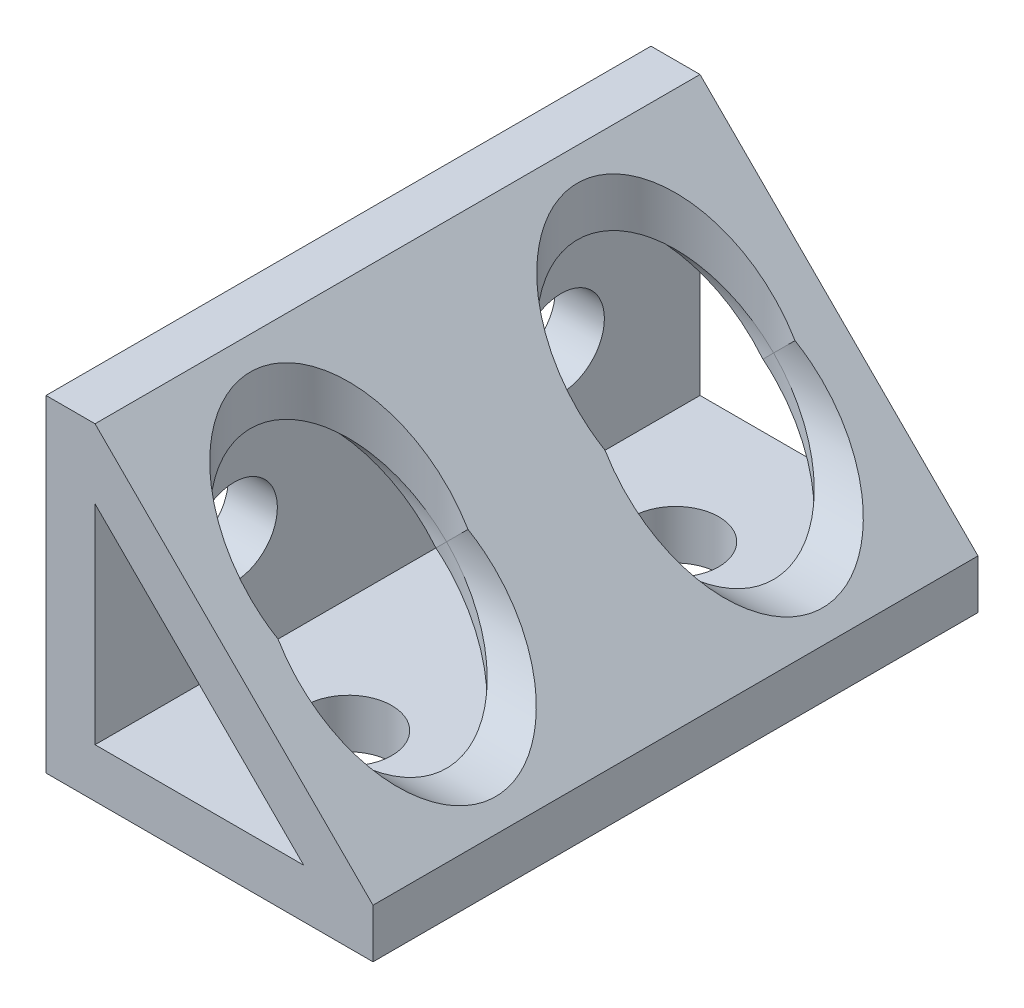
SolidWorks part; units mm, degrees
ref_plane "Front Plane" through (0, 0, 0) normal (0, 0, 1) x (1, 0, 0)
ref_plane "Top Plane" through (0, 0, 0) normal (0, 1, 0) x (1, 0, 0)
ref_plane "Right Plane" through (0, 0, 0) normal (1, 0, 0) x (0, 0, -1)
sketch "Sketch1" plane through (0, 0, 0) normal (0, 0, 1) x (1, 0, 0)
  line L0 (0, 10) -> (0, -10) construction
  line L1 (10, 0) -> (-10, 0) construction
  line L2 (-2.65, -10) -> (2.65, -10) construction
  line L3 (-10, -10) -> (-10, -7) construction
  line L4 (-6, -7) -> (6, -7) construction
  point P4 (0, 0)
  point P8 (0, 0)
  point P11 (0, -10)
  point P16 (0, -7)
  dimension "Length" = 20
  dimension "Clearance Hole" = 5.3
  dimension "Wall" = 3
  dimension "Access Hole" = 12
  dimension "For Rail Height" = 20
sketch "Sketch3" plane through (0, 0, 0) normal (1, 0, 0) x (0, 0, -1)
  line L0 (9.25, 0) -> (-9.25, 0) construction
  line L1 (-10, 0) -> (10, 0) construction
  point P3 (0, 0)
  point P7 (0, 0)
  dimension "Mounting Hole Center to Center" = 20
sketch "Sketch2" plane through (0, 0, 0) normal (0, 0, 1) x (1, 0, 0)
  line L0 (-10, 10) -> (-10, -10)
  line L1 (-10, -10) -> (10, -10)
  line L3 (-2.65, -10) -> (2.65, -10) construction
  line L4 (-10, -10) -> (-10, -7) construction
  line L5 (10, -10) -> (10, -7)
  line L6 (10, -7) -> (-7, 10)
  line L7 (-7, 10) -> (-10, 10)
  line L8 (-7, 5.7574) -> (-7, -7)
  line L9 (-7, -7) -> (5.7574, -7)
  line L10 (5.7574, -7) -> (5.7574, -7)
  line L11 (5.7574, -7) -> (-7, 5.7574)
  line L12 (-7, 5.7574) -> (-7, 5.7574)
extrude "Boss-Extrude1" add sketch "Sketch2" against normal mid plane 37
sketch "Sketch4" plane through (0, -10, 0) normal (0, -1, 0) x (1, 0, 0)
  line L0 (0, -9.25) -> (0, 9.25) construction
  line L1 (-2.65, -10) -> (2.65, -10) construction
  circle A0 centre (0, -10) radius 2.65
  circle A1 centre (0, 10) radius 2.65
extrude "Cut-Extrude1" cut sketch "Sketch4" against normal up to next (3 mm away)
sketch "Sketch6" plane through (0, -7, 0) normal (0, 1, 0) x (1, 0, 0)
  line L0 (0, -10) -> (0, 10) construction
  line L1 (-6, 0) -> (-6, -10) construction
  line L2 (-6, 0) -> (6, 0) construction
  circle A0 centre (0, -10) radius 6
extrude "Cut-Extrude2" cut sketch "Sketch6" along normal through all
ref_plane "Plane1" through (0, 0, 0) normal (0.7071, -0.7071, 0) x (-0.7071, -0.7071, 0)
mirror "Mirror1" about plane through (0, 0, 0) normal (0.7071, -0.7071, 0) of "Cut-Extrude2", "Cut-Extrude1"
mirror "Mirror2" about plane through (0, 0, 0) normal (0, 0, 1) of "Mirror1", "Cut-Extrude2"
sketch "Sketch7" plane through (-10, 0, 0) normal (-1, 0, 0) x (0, 0, 1)
  line L0 (-10, 2.65) -> (-10, -2.65) construction
  line L1 (10, 2.65) -> (10, -2.65) construction
  circle A0 centre (-10, 0) radius 2.65 construction
  circle A1 centre (10, 0) radius 2.65 construction
  circle A2 centre (10, 0) radius 2.65 construction
  point P11 (10, 0)
sketch "Sketch8" plane through (0, -10, 0) normal (0, -1, 0) x (1, 0, 0)
  line L0 (-2.65, 10) -> (2.65, 10) construction
  line L1 (0, 12.65) -> (0, 7.35) construction
  line L2 (0, -7.35) -> (0, -12.65) construction
  line L3 (-2.65, -10) -> (2.65, -10) construction
  circle A0 centre (0, 10) radius 2.65 construction
  circle A1 centre (0, 10) radius 2.65 construction
  circle A2 centre (0, -10) radius 2.65 construction
equation "\"D1@Boss-Extrude1\"= \"Thickness@Sketch3\" * 2"
